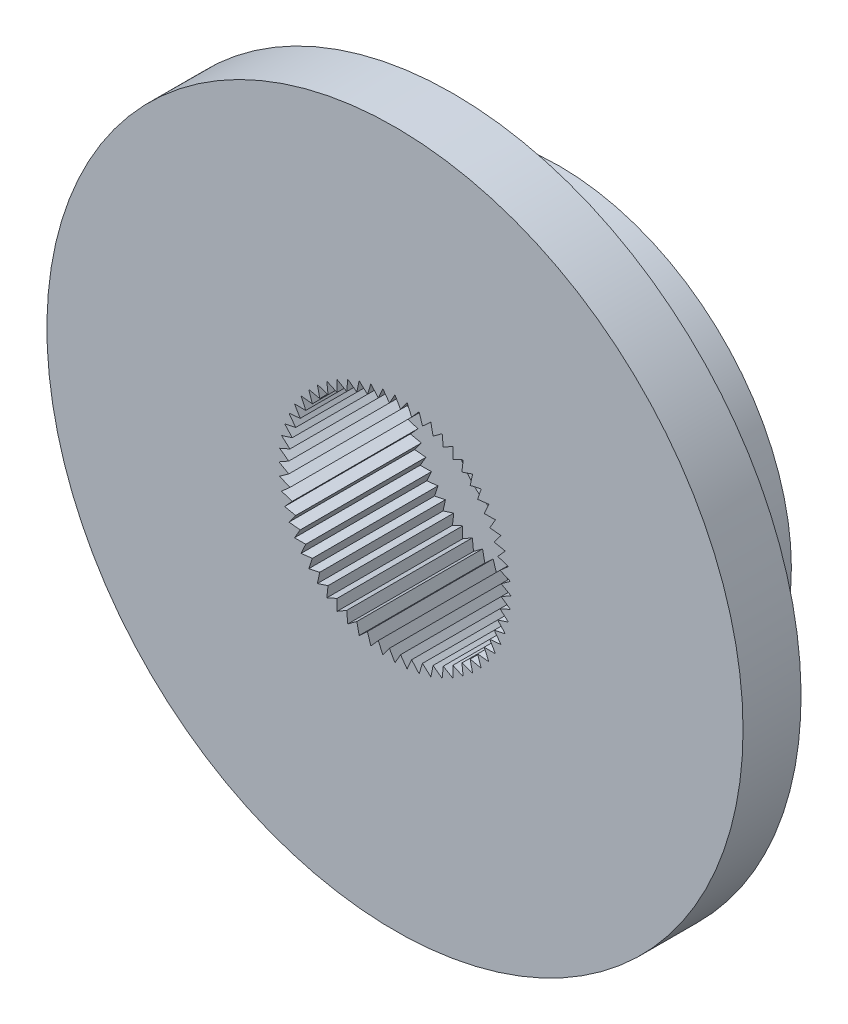
SolidWorks part; units mm, degrees
ref_plane "Plane1" through (0, 0, 0) normal (0, 0, 1) x (1, 0, 0)
ref_plane "Plane2" through (0, 0, 0) normal (0, 1, 0) x (1, 0, 0)
ref_plane "Plane3" through (0, 0, 0) normal (1, 0, 0) x (0, 0, -1)
sketch "Esquisse1" plane through (0, 0, 0) normal (0, 0, 1) x (1, 0, 0)
  line L0 (0, 0) -> (0, 4) construction
  line L1 (0, 0) -> (0.1655, 3.1579) construction
  line L2 (0, 0) -> (-0.1655, 3.1579) construction
  line L3 (0, 3) -> (-0.1439, 2.7462)
  line L4 (0, 3) -> (0.1439, 2.7462)
  line L5 (0.3136, 2.9836) -> (0.4302, 2.7161)
  line L6 (0.3136, 2.9836) -> (0.1439, 2.7462)
  line L7 (0.6237, 2.9344) -> (0.7118, 2.6563)
  line L8 (0.6237, 2.9344) -> (0.4302, 2.7161)
  line L9 (0.9271, 2.8532) -> (0.9855, 2.5673)
  line L10 (0.9271, 2.8532) -> (0.7118, 2.6563)
  line L11 (1.2202, 2.7406) -> (1.2485, 2.4503)
  line L12 (1.2202, 2.7406) -> (0.9855, 2.5673)
  line L13 (1.5, 2.5981) -> (1.4978, 2.3063)
  line L14 (1.5, 2.5981) -> (1.2485, 2.4503)
  line L15 (1.7634, 2.4271) -> (1.7306, 2.1372)
  line L16 (1.7634, 2.4271) -> (1.4978, 2.3063)
  line L17 (2.0074, 2.2294) -> (1.9445, 1.9445)
  line L18 (2.0074, 2.2294) -> (1.7306, 2.1372)
  line L19 (2.2294, 2.0074) -> (2.1372, 1.7306)
  line L20 (2.2294, 2.0074) -> (1.9445, 1.9445)
  line L21 (2.4271, 1.7634) -> (2.3063, 1.4978)
  line L22 (2.4271, 1.7634) -> (2.1372, 1.7306)
  line L23 (2.5981, 1.5) -> (2.4503, 1.2485)
  line L24 (2.5981, 1.5) -> (2.3063, 1.4978)
  line L25 (2.7406, 1.2202) -> (2.5673, 0.9855)
  line L26 (2.7406, 1.2202) -> (2.4503, 1.2485)
  line L27 (2.8532, 0.9271) -> (2.6563, 0.7118)
  line L28 (2.8532, 0.9271) -> (2.5673, 0.9855)
  line L29 (2.9344, 0.6237) -> (2.7161, 0.4302)
  line L30 (2.9344, 0.6237) -> (2.6563, 0.7118)
  line L31 (2.9836, 0.3136) -> (2.7462, 0.1439)
  line L32 (2.9836, 0.3136) -> (2.7161, 0.4302)
  line L33 (3, 0) -> (2.7462, -0.1439)
  line L34 (3, 0) -> (2.7462, 0.1439)
  line L35 (2.9836, -0.3136) -> (2.7161, -0.4302)
  line L36 (2.9836, -0.3136) -> (2.7462, -0.1439)
  line L37 (2.9344, -0.6237) -> (2.6563, -0.7118)
  line L38 (2.9344, -0.6237) -> (2.7161, -0.4302)
  line L39 (2.8532, -0.9271) -> (2.5673, -0.9855)
  line L40 (2.8532, -0.9271) -> (2.6563, -0.7118)
  line L41 (2.7406, -1.2202) -> (2.4503, -1.2485)
  line L42 (2.7406, -1.2202) -> (2.5673, -0.9855)
  line L43 (2.5981, -1.5) -> (2.3063, -1.4978)
  line L44 (2.5981, -1.5) -> (2.4503, -1.2485)
  line L45 (2.4271, -1.7634) -> (2.1372, -1.7306)
  line L46 (2.4271, -1.7634) -> (2.3063, -1.4978)
  line L47 (2.2294, -2.0074) -> (1.9445, -1.9445)
  line L48 (2.2294, -2.0074) -> (2.1372, -1.7306)
  line L49 (2.0074, -2.2294) -> (1.7306, -2.1372)
  line L50 (2.0074, -2.2294) -> (1.9445, -1.9445)
  line L51 (1.7634, -2.4271) -> (1.4978, -2.3063)
  line L52 (1.7634, -2.4271) -> (1.7306, -2.1372)
  line L53 (1.5, -2.5981) -> (1.2485, -2.4503)
  line L54 (1.5, -2.5981) -> (1.4978, -2.3063)
  line L55 (1.2202, -2.7406) -> (0.9855, -2.5673)
  line L56 (1.2202, -2.7406) -> (1.2485, -2.4503)
  line L57 (0.9271, -2.8532) -> (0.7118, -2.6563)
  line L58 (0.9271, -2.8532) -> (0.9855, -2.5673)
  line L59 (0.6237, -2.9344) -> (0.4302, -2.7161)
  line L60 (0.6237, -2.9344) -> (0.7118, -2.6563)
  line L61 (0.3136, -2.9836) -> (0.1439, -2.7462)
  line L62 (0.3136, -2.9836) -> (0.4302, -2.7161)
  line L63 (0, -3) -> (-0.1439, -2.7462)
  line L64 (0, -3) -> (0.1439, -2.7462)
  line L65 (-0.3136, -2.9836) -> (-0.4302, -2.7161)
  line L66 (-0.3136, -2.9836) -> (-0.1439, -2.7462)
  line L67 (-0.6237, -2.9344) -> (-0.7118, -2.6563)
  line L68 (-0.6237, -2.9344) -> (-0.4302, -2.7161)
  line L69 (-0.9271, -2.8532) -> (-0.9855, -2.5673)
  line L70 (-0.9271, -2.8532) -> (-0.7118, -2.6563)
  line L71 (-1.2202, -2.7406) -> (-1.2485, -2.4503)
  line L72 (-1.2202, -2.7406) -> (-0.9855, -2.5673)
  line L73 (-1.5, -2.5981) -> (-1.4978, -2.3063)
  line L74 (-1.5, -2.5981) -> (-1.2485, -2.4503)
  line L75 (-1.7634, -2.4271) -> (-1.7306, -2.1372)
  line L76 (-1.7634, -2.4271) -> (-1.4978, -2.3063)
  line L77 (-2.0074, -2.2294) -> (-1.9445, -1.9445)
  line L78 (-2.0074, -2.2294) -> (-1.7306, -2.1372)
  line L79 (-2.2294, -2.0074) -> (-2.1372, -1.7306)
  line L80 (-2.2294, -2.0074) -> (-1.9445, -1.9445)
  line L81 (-2.4271, -1.7634) -> (-2.3063, -1.4978)
  line L82 (-2.4271, -1.7634) -> (-2.1372, -1.7306)
  line L83 (-2.5981, -1.5) -> (-2.4503, -1.2485)
  line L84 (-2.5981, -1.5) -> (-2.3063, -1.4978)
  line L85 (-2.7406, -1.2202) -> (-2.5673, -0.9855)
  line L86 (-2.7406, -1.2202) -> (-2.4503, -1.2485)
  line L87 (-2.8532, -0.9271) -> (-2.6563, -0.7118)
  line L88 (-2.8532, -0.9271) -> (-2.5673, -0.9855)
  line L89 (-2.9344, -0.6237) -> (-2.7161, -0.4302)
  line L90 (-2.9344, -0.6237) -> (-2.6563, -0.7118)
  line L91 (-2.9836, -0.3136) -> (-2.7462, -0.1439)
  line L92 (-2.9836, -0.3136) -> (-2.7161, -0.4302)
  line L93 (-3, 0) -> (-2.7462, 0.1439)
  line L94 (-3, 0) -> (-2.7462, -0.1439)
  line L95 (-2.9836, 0.3136) -> (-2.7161, 0.4302)
  line L96 (-2.9836, 0.3136) -> (-2.7462, 0.1439)
  line L97 (-2.9344, 0.6237) -> (-2.6563, 0.7118)
  line L98 (-2.9344, 0.6237) -> (-2.7161, 0.4302)
  line L99 (-2.8532, 0.9271) -> (-2.5673, 0.9855)
  line L100 (-2.8532, 0.9271) -> (-2.6563, 0.7118)
  line L101 (-2.7406, 1.2202) -> (-2.4503, 1.2485)
  line L102 (-2.7406, 1.2202) -> (-2.5673, 0.9855)
  line L103 (-2.5981, 1.5) -> (-2.3063, 1.4978)
  line L104 (-2.5981, 1.5) -> (-2.4503, 1.2485)
  line L105 (-2.4271, 1.7634) -> (-2.1372, 1.7306)
  line L106 (-2.4271, 1.7634) -> (-2.3063, 1.4978)
  line L107 (-2.2294, 2.0074) -> (-1.9445, 1.9445)
  line L108 (-2.2294, 2.0074) -> (-2.1372, 1.7306)
  line L109 (-2.0074, 2.2294) -> (-1.7306, 2.1372)
  line L110 (-2.0074, 2.2294) -> (-1.9445, 1.9445)
  line L111 (-1.7634, 2.4271) -> (-1.4978, 2.3063)
  line L112 (-1.7634, 2.4271) -> (-1.7306, 2.1372)
  line L113 (-1.5, 2.5981) -> (-1.2485, 2.4503)
  line L114 (-1.5, 2.5981) -> (-1.4978, 2.3063)
  line L115 (-1.2202, 2.7406) -> (-0.9855, 2.5673)
  line L116 (-1.2202, 2.7406) -> (-1.2485, 2.4503)
  line L117 (-0.9271, 2.8532) -> (-0.7118, 2.6563)
  line L118 (-0.9271, 2.8532) -> (-0.9855, 2.5673)
  line L119 (-0.6237, 2.9344) -> (-0.4302, 2.7161)
  line L120 (-0.6237, 2.9344) -> (-0.7118, 2.6563)
  line L121 (-0.3136, 2.9836) -> (-0.1439, 2.7462)
  line L122 (-0.3136, 2.9836) -> (-0.4302, 2.7161)
  dimension "D2" = 6
sketch "Esquisse2" plane through (0, 0, 0) normal (0, 0, 1) x (1, 0, 0)
  line L0 (0, 0) -> (0, -14) construction
  line L1 (1.5, -5.8095) -> (1.5, -8.8741)
  line L2 (-1.5, -5.8095) -> (-1.5, -8.8741)
  arc A0 (-1.5, -8.8741) -> (1.5, -8.8741) centre (0, 0) ccw
  arc A1 (1.5, -5.8095) -> (-1.5, -5.8095) centre (0, 0) ccw
  dimension "D1" = 12
  dimension "D3" = 9
  dimension "D2" = 3
extrude "Base-Extrusion" add sketch "Esquisse2" along normal blind 2.75
sketch "Esquisse3" plane through (0, 0, 2.75) normal (0, 0, 1) x (1, 0, 0)
  circle A0 centre (0, 0) radius 9
extrude "Boss.-Extru.1" add sketch "Esquisse3" along normal blind 1.5
extrude "Enlèv. mat.-Extru.2" cut sketch "Esquisse1" along normal through all
sketch "Esquisse5" plane through (0, 0, 0) normal (0, 0, -1) x (-1, 0, 0)
  circle A0 centre (0, 0) radius 4
extrude "Boss.-Extru.2" add sketch "Esquisse5" against normal blind 1
sketch "Esquisse6" plane through (0, 0, 0) normal (0, 0, -1) x (-1, 0, 0)
  circle A0 centre (0, 0) radius 2.5
  dimension "D1" = 5
extrude "Boss.-Extru.3" add sketch "Esquisse6" along normal blind 1.5
sketch "Esquisse7" plane through (0, 0, -1.5) normal (0, 0, -1) x (-1, 0, 0)
  circle A0 centre (0, 0) radius 1.75
  dimension "D1" = 3.5
extrude "Enlèv. mat.-Extru.3" cut sketch "Esquisse7" against normal through all
